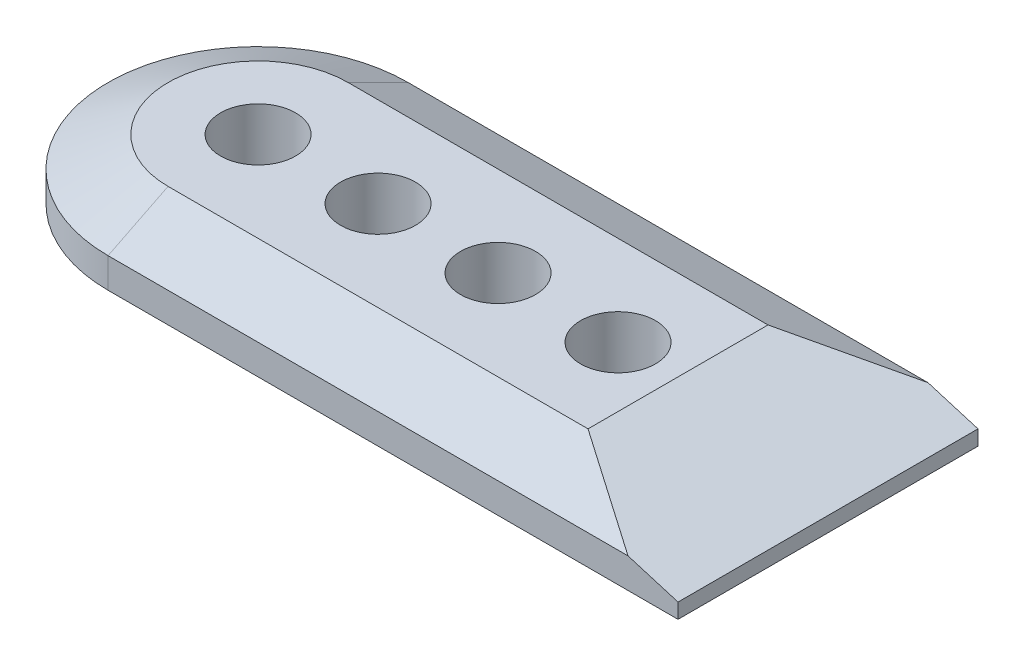
SolidWorks part; units mm, degrees
ref_plane "Front Plane" through (0, 0, 0) normal (0, 0, 1) x (1, 0, 0)
ref_plane "Top Plane" through (0, 0, 0) normal (0, 1, 0) x (1, 0, 0)
ref_plane "Right Plane" through (0, 0, 0) normal (1, 0, 0) x (0, 0, -1)
sketch "Sketch1" plane through (0, 0, 0) normal (0, 1, 0) x (1, 0, 0)
  line L3 (0, -12.5) -> (0, 12.5)
  line L7 (0, 12.5) -> (-47.5, 12.5)
  line L8 (0, -12.5) -> (-47.5, -12.5)
  circle A7 centre (-47.5, 0) radius 3.125
  circle A8 centre (-37.5, 0) radius 3.125
  circle A9 centre (-27.5, 0) radius 3.125
  circle A10 centre (-17.5, 0) radius 3.125
  arc A11 (-47.5, 12.5) -> (-47.5, -12.5) centre (-47.5, 0) ccw
  point P2 (0, 0)
  point P6 (0, 0)
  point P7 (-47.4742, 12.5)
  point P8 (-60, 0)
  point P11 (0, 0)
  dimension "D1" = 10
  dimension "D5" = 6.25
  dimension "D3" = 12.5
  dimension "D2" = 60
  dimension "D4" = 4
  dimension "D6" = 12.5
extrude "Boss-Extrude1" add sketch "Sketch1" along normal blind 5
chamfer "Chamfer1" distance 2.5 distance2 5 3 edges at (-23.75, 5, 12.5) (-60, 5, 0) (-23.75, 5, -12.5)
chamfer "Chamfer2" distance 3.75 distance2 12.5 1 edges at (0, 5, 0)
